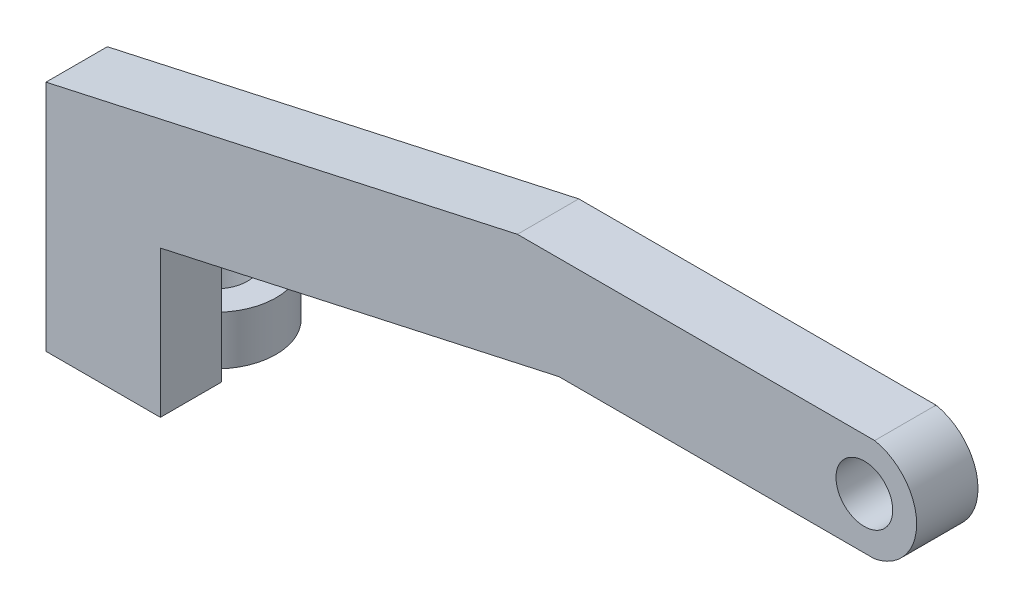
SolidWorks part; units mm, degrees
ref_plane "Front Plane" through (0, 0, 0) normal (0, 0, 1) x (1, 0, 0)
ref_plane "Top Plane" through (0, 0, 0) normal (0, 1, 0) x (1, 0, 0)
ref_plane "Right Plane" through (0, 0, 0) normal (1, 0, 0) x (0, 0, -1)
sketch "Sketch1" plane through (0, 0, 0) normal (0, 0, 1) x (1, 0, 0)
  line L0 (24.6154, 0) -> (37.4796, 0)
  line L1 (37.4796, 4.1782) -> (22.9231, 4.1782)
  line L7 (37.0589, 2.0891) -> (35.9037, 2.0891) construction
  line L10 (24.6154, 0) -> (8.3762, -3.5804)
  line L11 (3.7158, -0.0566) -> (22.9231, 4.1782)
  line L13 (3.7158, -0.0566) -> (3.7158, -9.5566)
  line L14 (8.3762, -3.5804) -> (8.3762, -9.5566)
  line L15 (3.7158, -9.5566) -> (8.3762, -9.5566)
  arc A0 (37.4796, 0) -> (37.4796, 4.1782) centre (37.0589, 2.0891) ccw
  circle A1 centre (37.0589, 2.0891) radius 1.1551
  dimension "D1" = 9.5
extrude "Boss-Extrude1" add sketch "Sketch1" along normal blind 2.5
sketch "Sketch4" plane through (0, -9.5566, 0) normal (0, -1, 0) x (1, 0, 0)
  line L0 (3.7158, 0) -> (8.3762, 0) construction
  line L1 (3.7158, 1.25) -> (8.3762, 1.25) construction
  line L2 (3.7158, 2.5) -> (3.7158, 0) construction
  line L3 (8.3762, 2.5) -> (8.3762, 0) construction
  circle A3 centre (6.046, -2.0774) radius 1.3
  arc A4 (4.7158, 0) -> (7.3762, 0) centre (6.046, -2.0774) ccw
  point P0 (0, 0)
  line M1 (3.7158, 0) -> (8.3762, 0)
extrude "Boss-Extrude5" add sketch "Sketch4" against normal blind 2 separate body contours A4 A3 M1
